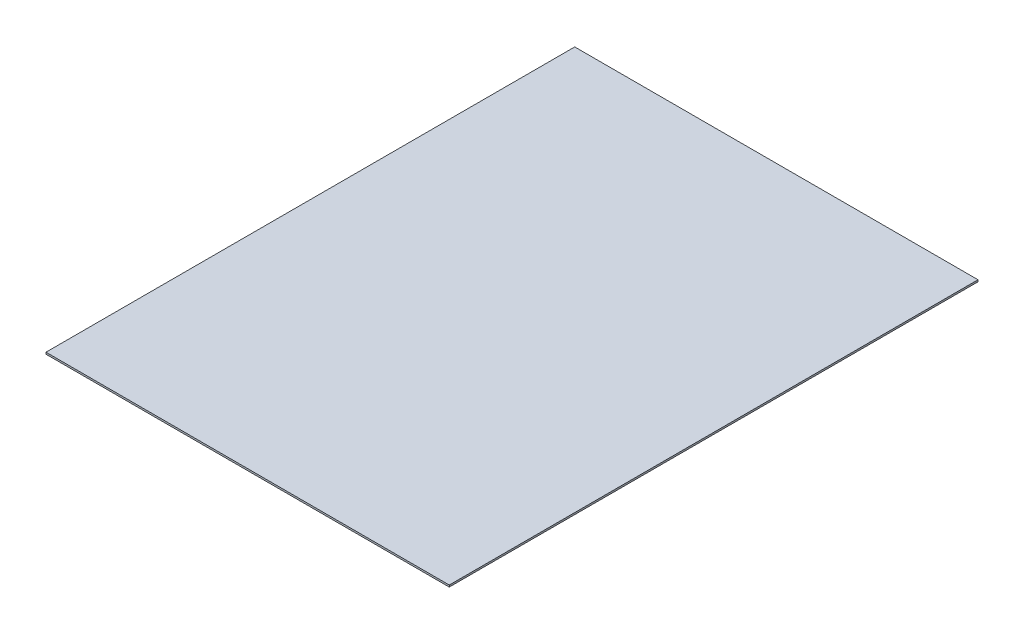
SolidWorks part; units mm, degrees
ref_plane "Front Plane" through (0, 0, 0) normal (0, 0, 1) x (1, 0, 0)
ref_plane "Top Plane" through (0, 0, 0) normal (0, 1, 0) x (1, 0, 0)
ref_plane "Right Plane" through (0, 0, 0) normal (1, 0, 0) x (0, 0, -1)
sketch "Sketch1" plane through (0, 0, 0) normal (0, 1, 0) x (1, 0, 0)
  line L1 (-225, -295) -> (225, -295)
  line L2 (-225, -295) -> (-225, 295)
  line L3 (-225, 295) -> (225, 295)
  line L4 (225, -295) -> (225, 295)
  line L5 (-225, -295) -> (225, 295) construction
  line L6 (-225, 295) -> (225, -295) construction
  point P0 (0, 0)
  dimension "D1" = 450
  dimension "D2" = 590
extrude "Boss-Extrude1" add sketch "Sketch1" along normal blind 2
